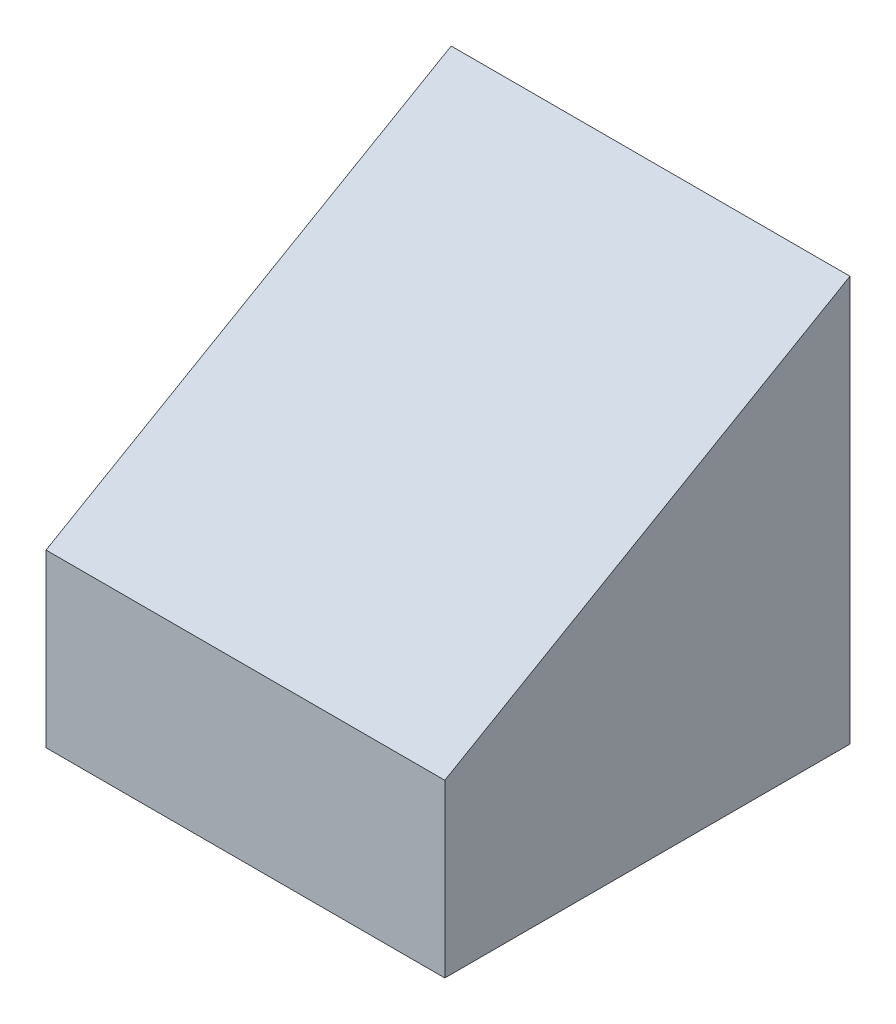
SolidWorks part; units mm, degrees
ref_plane "Front Plane" through (0, 0, 0) normal (0, 0, 1) x (1, 0, 0)
ref_plane "Top Plane" through (0, 0, 0) normal (0, 1, 0) x (1, 0, 0)
ref_plane "Right Plane" through (0, 0, 0) normal (1, 0, 0) x (0, 0, -1)
sketch "Sketch1" plane through (0, 0, 0) normal (1, 0, 0) x (0, 0, -1)
  line L0 (0, 0) -> (0, 25.4)
  line L1 (0, 25.4) -> (-25.4, 10.7353)
  line L2 (-25.4, 10.7353) -> (-25.4, 0)
  line L3 (-25.4, 0) -> (0, 0)
  dimension "D1" = 30
  dimension "D2" = 25.4
  dimension "D3" = 25.4
extrude "Boss-Extrude1" add sketch "Sketch1" along normal mid plane 25
hole_wizard "#10-24 Tapped Hole2" positions "Sketch4" profile "Sketch3" tap size "#10-24" standard "ANSI Inch"
sketch "Sketch4" plane through (0, 0, 0) normal (0, -1, 0) x (-1, 0, 0)
  line L3 (-12.5, 0) -> (12.5, 0) construction
  point P0 (105.781, 37.5771)
  point P1 (0, -12.7)
  point P9 (0, 0)
  point P10 (0, 0)
  point P12 (0, 0)
  point P17 (0, -20)
  dimension "D1" = 12.7
sketch "Sketch3" plane through (-105.781, 0, -37.5771) normal (1, 0, 0) x (0, 0, -1)
  line L0 (0, 0) -> (0, 13.9708)
  line L1 (0, 13.9708) -> (1.8986, 12.83)
  line L2 (1.8986, 12.83) -> (1.8986, 0)
  line L5 (1.8986, 0) -> (0, 0)
  line L10 (0, 13.9708) -> (-1.8987, 12.83) construction
  line L11 (0, -6.35) -> (0, 107.95) construction
  dimension "Tap Drill Dia." = 3.7973
  dimension "Tap Drill Depth" = 12.83
  dimension "Drill Angle" = 118
cosmetic thread "Hole Thread1" parameters "D1"=9.65, "D2"=4.826
